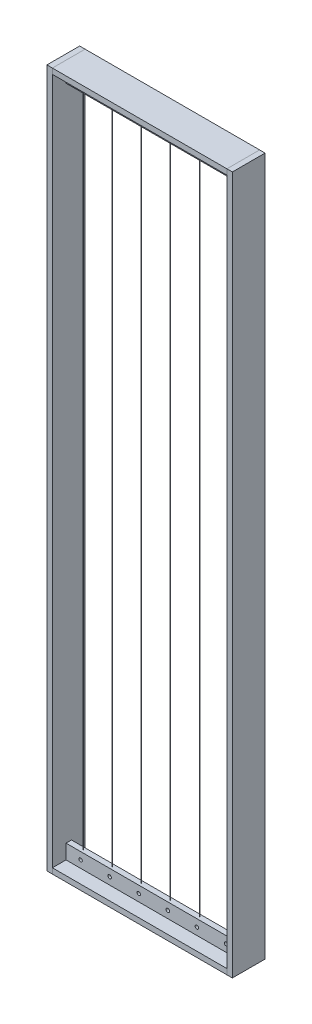
SolidWorks part; units mm, degrees
ref_plane "Front Plane" through (0, 0, 0) normal (0, 0, 1) x (1, 0, 0)
ref_plane "Top Plane" through (0, 0, 0) normal (0, 1, 0) x (1, 0, 0)
ref_plane "Right Plane" through (0, 0, 0) normal (1, 0, 0) x (0, 0, -1)
sketch "Sketch1" plane through (0, 0, 0) normal (0, 1, 0) x (1, 0, 0)
  line L1 (-1137.5166, -14.4648) -> (-527.9166, -14.4648)
  line L2 (-1137.5166, -14.4648) -> (-1137.5166, 99.8352)
  line L3 (-1137.5166, 99.8352) -> (-527.9166, 99.8352)
  line L4 (-527.9166, -14.4648) -> (-527.9166, 99.8352)
  dimension "D1" = 609.6
  dimension "D2" = 114.3
extrude "Boss-Extrude1" add sketch "Sketch1" along normal blind 19.05
sketch "Sketch2" plane through (0, 0, 0) normal (0, 1, 0) x (1, 0, 0)
  line L1 (-527.9166, -14.4648) -> (-508.8666, -14.4648)
  line L2 (-527.9166, -14.4648) -> (-527.9166, 99.8352)
  line L3 (-527.9166, 99.8352) -> (-508.8666, 99.8352)
  line L4 (-508.8666, -14.4648) -> (-508.8666, 99.8352)
  line L5 (-1137.5166, -14.4648) -> (-1156.5666, -14.4648)
  line L6 (-1137.5166, -14.4648) -> (-1137.5166, 99.8352)
  line L7 (-1137.5166, 99.8352) -> (-1156.5666, 99.8352)
  line L8 (-1156.5666, -14.4648) -> (-1156.5666, 99.8352)
  dimension "D1" = 19.05
  dimension "D2" = 114.3
  dimension "D3" = 19.05
extrude "Boss-Extrude2" add sketch "Sketch2" along normal blind 2438.4 separate body
sketch "Sketch3" plane through (-1137.5166, 0, 0) normal (1, 0, 0) x (0, 0, -1)
  line L1 (-14.4648, 2438.4) -> (99.8352, 2438.4)
  line L2 (-14.4648, 2438.4) -> (-14.4648, 2419.35)
  line L3 (-14.4648, 2419.35) -> (99.8352, 2419.35)
  line L4 (99.8352, 2438.4) -> (99.8352, 2419.35)
  dimension "D1" = 19.05
extrude "Boss-Extrude3" add sketch "Sketch3" along normal blind 609.6 separate body
sketch "Sketch4" plane through (0, 19.05, 0) normal (0, 1, 0) x (1, 0, 0)
  line L0 (-1137.5166, 99.8352) -> (-1137.5166, -14.4648) construction
  line L1 (-1137.5166, 33.1602) -> (-527.9166, 33.1602)
  line L2 (-1137.5166, 33.1602) -> (-1137.5166, 52.2102)
  line L3 (-1137.5166, 52.2102) -> (-527.9166, 52.2102)
  line L4 (-527.9166, 33.1602) -> (-527.9166, 52.2102)
  line L5 (-527.9166, -14.4648) -> (-527.9166, 99.8352) construction
  point P8 (-1137.5166, 42.6852)
  dimension "D1" = 19.05
extrude "Boss-Extrude4" add sketch "Sketch4" along normal blind 50.8 separate body
sketch "Sketch5" plane through (-1137.5166, 0, 0) normal (1, 0, 0) x (0, 0, -1)
  line L0 (-14.4648, 2419.35) -> (99.8352, 2419.35) construction
  line L1 (33.1602, 2419.35) -> (52.2102, 2419.35)
  line L2 (33.1602, 2419.35) -> (33.1602, 2368.55)
  line L3 (33.1602, 2368.55) -> (52.2102, 2368.55)
  line L4 (52.2102, 2419.35) -> (52.2102, 2368.55)
  point P6 (42.6852, 2419.35)
  dimension "D1" = 19.05
  dimension "D2" = 50.8
extrude "Boss-Extrude5" add sketch "Sketch5" along normal up to next (609.6 mm away) separate body
sketch "Sketch7" plane through (0, 0, -33.1602) normal (0, 0, 1) x (1, 0, 0)
  line L0 (-1137.5166, 2419.35) -> (-1137.5166, 2368.55) construction
  line L4 (-1137.5166, 69.85) -> (-527.9166, 69.85) construction
  line L5 (-1137.5166, 69.85) -> (-1137.5166, 19.05) construction
  circle A0 centre (-1086.7166, 2393.95) radius 3.175
  circle A1 centre (-985.1166, 2393.95) radius 3.175
  circle A2 centre (-883.5166, 2393.95) radius 3.175
  circle A3 centre (-781.9166, 2393.95) radius 3.175
  circle A4 centre (-680.3166, 2393.95) radius 3.175
  circle A5 centre (-578.7166, 2393.95) radius 3.175
  circle A6 centre (-1086.7166, 44.45) radius 6.0716
  circle A7 centre (-985.1166, 44.45) radius 6.0716
  circle A8 centre (-883.5166, 44.45) radius 6.0716
  circle A9 centre (-781.9166, 44.45) radius 6.0716
  circle A10 centre (-680.3166, 44.45) radius 6.0716
  circle A11 centre (-578.7166, 44.45) radius 6.0716
  point P5 (-1137.5166, 2393.95)
  dimension "D2" = 6.35
  dimension "D3" = 6.35
  dimension "D1" = 50.8
  dimension "D4" = 101.6
  dimension "D6" = 25.4
  dimension "D7" = 50.8
  dimension "D5" = 3
  dimension "D8" = 6
extrude "Cut-Extrude1" cut sketch "Sketch7" against normal blind 50.8
sketch "Sketch8" plane through (0, 2368.55, 0) normal (0, -1, 0) x (1, 0, 0)
  line L0 (-1086.9701, -52.2102) -> (-1086.9701, -33.1602) construction
  line L1 (-527.9166, -52.2102) -> (-1137.5166, -52.2102) construction
  line L2 (-1137.5166, -33.1602) -> (-527.9166, -33.1602) construction
  line L3 (-1086.9701, -42.6852) -> (-1081.7719, -42.6852) construction
  circle A0 centre (-1086.9701, -42.2026) radius 0.254
  circle A1 centre (-1086.4876, -42.6852) radius 0.254
  circle A2 centre (-1086.9701, -43.1678) radius 0.254
  circle A3 centre (-1087.4527, -42.6852) radius 0.254
  circle A4 centre (-985.8527, -42.6852) radius 0.254
  circle A5 centre (-985.3701, -43.1678) radius 0.254
  circle A6 centre (-985.3701, -42.2026) radius 0.254
  circle A7 centre (-984.8876, -42.6852) radius 0.254
  circle A8 centre (-884.2527, -42.6852) radius 0.254
  circle A9 centre (-883.7701, -43.1678) radius 0.254
  circle A10 centre (-883.7701, -42.2026) radius 0.254
  circle A11 centre (-883.2876, -42.6852) radius 0.254
  circle A12 centre (-782.6527, -42.6852) radius 0.254
  circle A13 centre (-782.1701, -43.1678) radius 0.254
  circle A14 centre (-782.1701, -42.2026) radius 0.254
  circle A15 centre (-781.6876, -42.6852) radius 0.254
  circle A16 centre (-681.0527, -42.6852) radius 0.254
  circle A17 centre (-680.5701, -43.1678) radius 0.254
  circle A18 centre (-680.5701, -42.2026) radius 0.254
  circle A19 centre (-680.0876, -42.6852) radius 0.254
  circle A20 centre (-579.4527, -42.6852) radius 0.254
  circle A21 centre (-578.9701, -43.1678) radius 0.254
  circle A22 centre (-578.9701, -42.2026) radius 0.254
  circle A23 centre (-578.4876, -42.6852) radius 0.254
  point P10 (0, 0)
  point P12 (0, 0)
  point P19 (-1086.9701, -42.6852)
  point P59 (0, 0)
  point P60 (0, 0)
  dimension "D1" = 0.508
  dimension "D3" = 6
  dimension "D2" = 4
extrude "Boss-Extrude6" add sketch "Sketch8" along normal up to next contours A3 | A0 | A1 | A2
